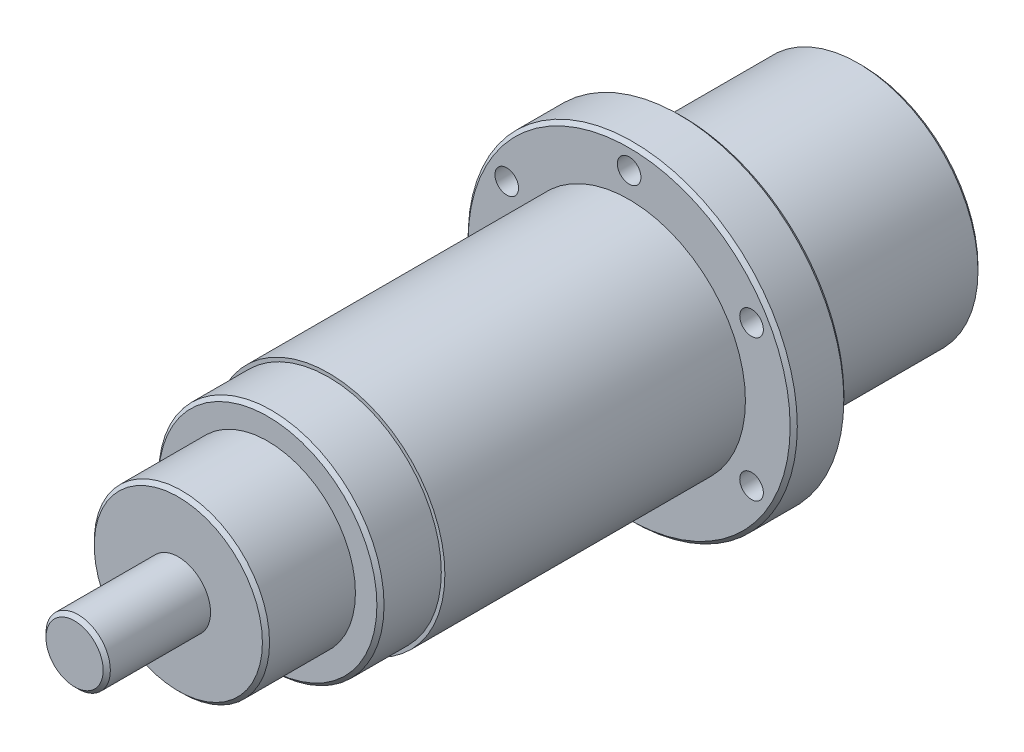
SolidWorks part; units mm, degrees
material "1.6523 (20NiCrMoS2-2)"
ref_plane "前视基准面" through (0, 0, 0) normal (0, 0, 1) x (1, 0, 0)
ref_plane "上视基准面" through (0, 0, 0) normal (0, 1, 0) x (1, 0, 0)
ref_plane "右视基准面" through (0, 0, 0) normal (1, 0, 0) x (0, 0, -1)
other "Configuration Table"
sketch "草图1" plane through (0, 0, 0) normal (0, 0, 1) x (1, 0, 0)
  circle A0 centre (0, 0) radius 33.5
  dimension "D1" = 67
extrude "凸台-拉伸1" add sketch "草图1" along normal blind 50
sketch "草图2" plane through (0, 0, 50) normal (0, 0, 1) x (1, 0, 0)
  circle A0 centre (0, 0) radius 46
  dimension "D1" = 92
extrude "凸台-拉伸2" add sketch "草图2" along normal blind 15
sketch "草图3" plane through (0, 0, 65) normal (0, 0, 1) x (1, 0, 0)
  circle A0 centre (0, 0) radius 32.5
  dimension "D1" = 65
extrude "凸台-拉伸3" add sketch "草图3" along normal blind 84
sketch "草图4" plane through (0, 0, 149) normal (0, 0, 1) x (1, 0, 0)
  circle A0 centre (0, 0) radius 31.5
  dimension "D1" = 63
extrude "凸台-拉伸4" add sketch "草图4" along normal blind 17
sketch "草图5" plane through (0, 0, 166) normal (0, 0, 1) x (1, 0, 0)
  circle A0 centre (0, 0) radius 24.5
  dimension "D1" = 49
extrude "凸台-拉伸5" add sketch "草图5" along normal blind 25
sketch "草图6" plane through (0, 0, 191) normal (0, 0, 1) x (1, 0, 0)
  circle A0 centre (0, 0) radius 9
  dimension "D1" = 18
extrude "凸台-拉伸6" add sketch "草图6" along normal blind 29
sketch "草图7" plane through (0, 0, 0) normal (0, 0, -1) x (-1, 0, 0)
  circle A0 centre (0, 0) radius 15
  dimension "D1" = 30
extrude "切除-拉伸1" cut sketch "草图7" against normal blind 20
chamfer "倒角1" distance 1 angle 45 6 edges at (9, 0, 220) (24.5, 0, 191) (31.5, 0, 166) (46, 0, 65) (46, 0, 50) (33.5, 0, 0)
sketch "草图8" plane through (0, 0, 50) normal (0, 0, -1) x (-1, 0, 0)
  line L0 (0, 0) -> (0, 45) construction
  circle A0 centre (0, 0) radius 45 construction
  circle A1 centre (0, 39.5) radius 5.5
  circle A2 centre (34.208, 19.75) radius 5.5
  circle A3 centre (34.208, -19.75) radius 5.5
  circle A4 centre (0, -39.5) radius 5.5
  circle A5 centre (-34.208, -19.75) radius 5.5
  circle A6 centre (-34.208, 19.75) radius 5.5
  point P20 (0, 0)
  dimension "D2" = 11
  dimension "D1" = 39.5
  dimension "D3" = 6
extrude "切除-拉伸2" cut sketch "草图8" against normal blind 7
sketch "草图9" plane through (0, 0, 57) normal (0, 0, -1) x (-1, 0, 0)
  circle A0 centre (0, 39.5) radius 3.3
  circle A1 centre (34.208, 19.75) radius 3.3
  circle A2 centre (34.208, -19.75) radius 3.3
  circle A3 centre (0, -39.5) radius 3.3
  circle A4 centre (-34.208, -19.75) radius 3.3
  circle A5 centre (-34.208, 19.75) radius 3.3
  point P15 (0, 0)
  dimension "D1" = 6.6
  dimension "D2" = 6
extrude "切除-拉伸3" cut sketch "草图9" against normal through all
